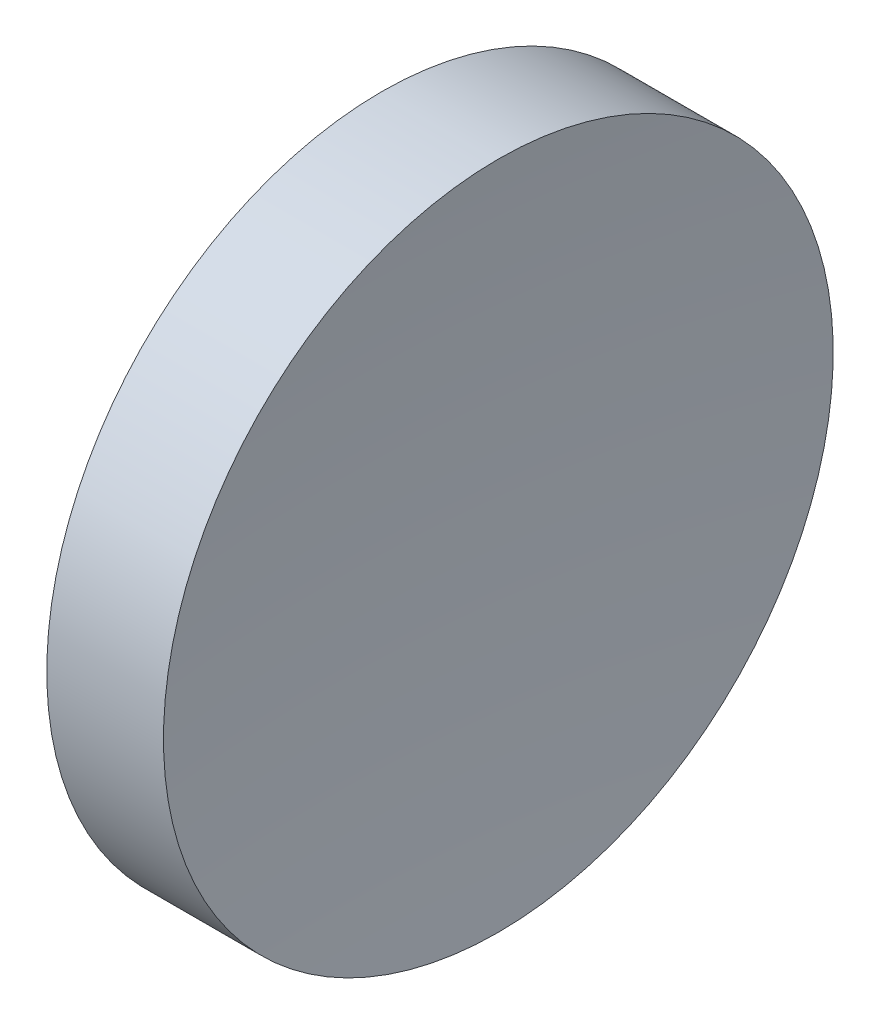
SolidWorks part; units mm, degrees
ref_plane "前视基准面" through (0, 0, 0) normal (0, 0, 1) x (1, 0, 0)
ref_plane "上视基准面" through (0, 0, 0) normal (0, 1, 0) x (1, 0, 0)
ref_plane "右视基准面" through (0, 0, 0) normal (1, 0, 0) x (0, 0, -1)
sketch "草图1" plane through (0, 0, 0) normal (0, 0, 1) x (1, 0, 0)
  line L0 (21.506, 13.0311) -> (26.997, 13.0311) construction
  line L1 (22.4242, 13.0311) -> (22.4242, 18.0311)
  line L2 (22.4242, 18.0311) -> (24.1669, 18.0311)
  line L3 (23.9242, 13.0311) -> (22.4242, 13.0311)
  arc A0 (24.1669, 18.0311) -> (23.9242, 13.0311) centre (75.5642, 13.0311) ccw
revolve "旋转1" add sketch "草图1" angle 360 about L0
